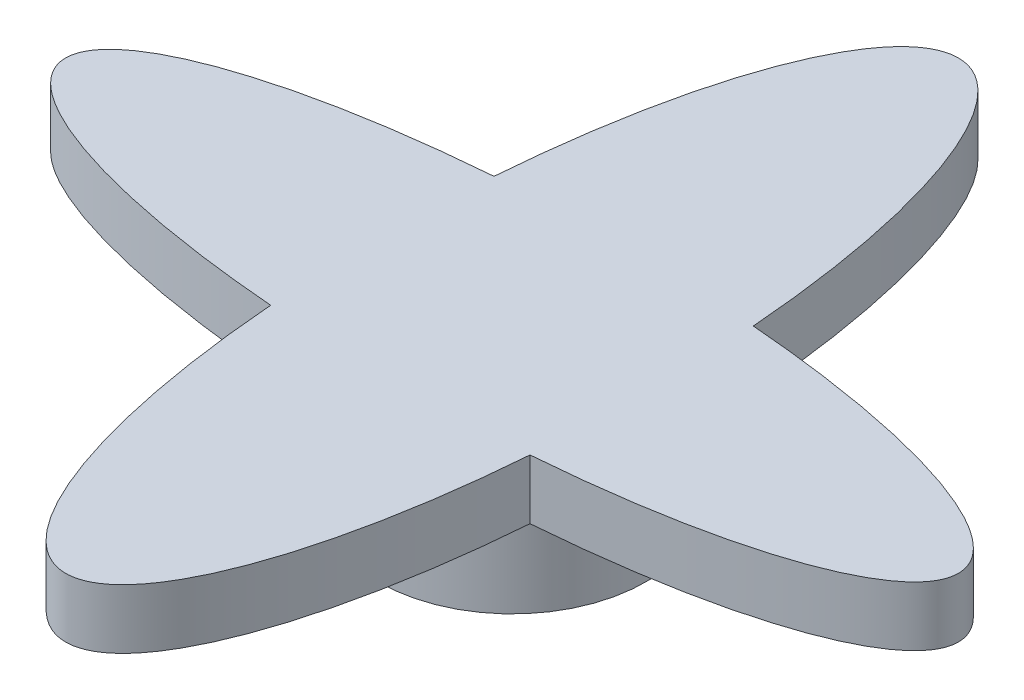
SolidWorks part; units mm, degrees
ref_plane "Front Plane" through (0, 0, 0) normal (0, 0, 1) x (1, 0, 0)
ref_plane "Top Plane" through (0, 0, 0) normal (0, 1, 0) x (1, 0, 0)
ref_plane "Right Plane" through (0, 0, 0) normal (1, 0, 0) x (0, 0, -1)
sketch "Sketch1" plane through (0, 0, 0) normal (0, 1, 0) x (1, 0, 0)
  circle A0 centre (0, 0) radius 4.5
  dimension "D1" = 9
extrude "Boss-Extrude1" add sketch "Sketch1" along normal blind 3.5
sketch "Sketch2" plane through (0, 3.5, 0) normal (0, 1, 0) x (1, 0, 0)
  line L5 (4.3569, 3.7523) -> (7.9895, 6.8807) construction
  circle A2 centre (0, 0) radius 4.5 construction
  ellipse E0 centre (0, 0) end of major axis (-15, 0) minor radius 3.9214 (-4.3569, 3.7523) -> (-4.3569, -3.7523) ccw
  ellipse E1 centre (0, 0) end of major axis (0, 15) minor radius 4.5 (-4.3569, -3.7523) -> (4.3569, -3.7523) ccw
  ellipse E2 centre (0, 0) end of major axis (0, 15) minor radius 4.5 (4.3569, 3.7523) -> (-4.3569, 3.7523) ccw
  ellipse E3 centre (0, 0) end of major axis (-15, 0) minor radius 3.9214 (4.3569, -3.7523) -> (4.3569, 3.7523) ccw
extrude "Boss-Extrude2" add sketch "Sketch2" along normal blind 2
sketch3d "3DSketch1"
  line L0 (0, 0, 0) -> (15.0291, 0, 0) construction
  line L1 (15.0291, 0, 0) -> (-14.9804, 0, 0) construction
sketch "Sketch3" plane through (0, 5.5, 0) normal (0, 1, 0) x (1, 0, 0)
  line L0 (15, 0) -> (-15, 0) construction
  ellipse E0 centre (0, 0) end of major axis (-15, 0) minor radius 3.9214 (4.3569, -3.7523) -> (4.3569, 3.7523) ccw construction
  ellipse E1 centre (0, 0) end of major axis (-15, 0) minor radius 3.9214 (-4.3569, 3.7523) -> (-4.3569, -3.7523) ccw construction
  point P17 (0, 0)
